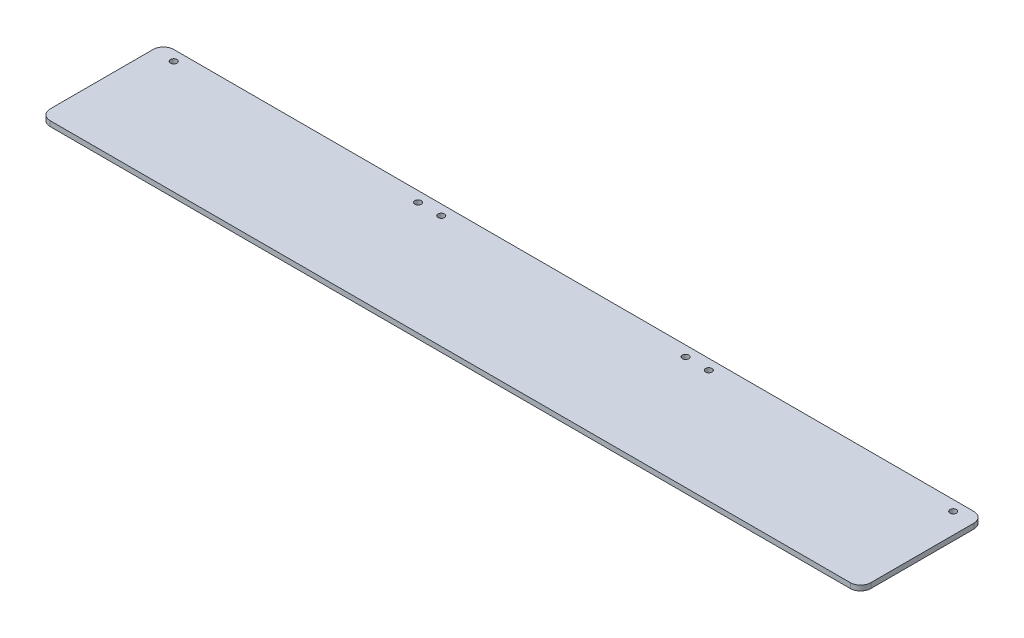
SolidWorks part; units mm, degrees
material "PC High Viscosity"
ref_plane "Front Plane" through (0, 0, 0) normal (0, 0, 1) x (1, 0, 0)
ref_plane "Top Plane" through (0, 0, 0) normal (0, 1, 0) x (1, 0, 0)
ref_plane "Right Plane" through (0, 0, 0) normal (1, 0, 0) x (0, 0, -1)
sketch "Sketch1" plane through (0, 0, 0) normal (0, 1, 0) x (1, 0, 0)
  line L0 (654.05, 279.4) -> (711.2, 279.4) construction
  line L1 (25.4, 0) -> (2000.25, 0)
  line L2 (0, 25.4) -> (0, 279.4)
  line L3 (25.4, 304.8) -> (2000.25, 304.8)
  line L4 (2025.65, 25.4) -> (2025.65, 279.4)
  line L17 (1012.825, 304.8) -> (1012.825, 0) construction
  line L28 (50.8, 279.4) -> (50.8, 304.8) construction
  line L30 (1974.85, 279.4) -> (1974.85, 304.8) construction
  line L32 (1371.6, 279.4) -> (1314.45, 279.4) construction
  arc A0 (2000.25, 304.8) -> (2025.65, 279.4) centre (2000.25, 279.4) cw
  arc A3 (0, 279.4) -> (25.4, 304.8) centre (25.4, 279.4) cw
  circle A4 centre (50.8, 279.4) radius 7.9375
  circle A10 centre (654.05, 279.4) radius 7.9375
  circle A12 centre (711.2, 279.4) radius 7.9375
  circle A42 centre (1314.45, 279.4) radius 7.9375
  circle A43 centre (1371.6, 279.4) radius 7.9375
  circle A45 centre (1974.85, 279.4) radius 7.9375
  circle A46 centre (654.05, 88.9) radius 7.9375 [skipped]
  circle A47 centre (711.2, 88.9) radius 7.9375 [skipped]
  arc A50 (0, 25.4) -> (25.4, 0) centre (25.4, 25.4) ccw
  arc A51 (2025.65, 25.4) -> (2000.25, 0) centre (2000.25, 25.4) cw
  point P7 (2025.65, 304.8)
  point P12 (0, 0)
  point P15 (0, 304.8)
  point P93 (1371.6, 303.2125)
  point P105 (1371.6, 303.2125)
  point P112 (1371.6, 303.2125)
  point P119 (1371.6, 303.2125)
  point P126 (1371.6, 303.2125)
  point P133 (1371.6, 303.2125)
  point P140 (1371.6, 303.2125)
  point P147 (1371.6, 303.2125)
  point P154 (1371.6, 303.2125)
  point P161 (1371.6, 303.2125)
  point P168 (1371.6, 303.2125)
  point P175 (1371.6, 303.2125)
  point P182 (1371.6, 303.2125)
  point P189 (1371.6, 303.2125)
  point P196 (1371.6, 303.2125)
  point P203 (1371.6, 303.2125)
  point P210 (1371.6, 303.2125)
  point P217 (1371.6, 303.2125)
  point P224 (1371.6, 303.2125)
  point P231 (1371.6, 303.2125)
  dimension "D3" = 25.4
  dimension "D6" = 15.875
  dimension "D18" = 2
  dimension "D8" = 25.4
  dimension "D9" = 25.4
  dimension "D1" = 2025.65
  dimension "D2" = 304.8
  dimension "D4" = 50.8
  dimension "D5" = 25.4
  dimension "D20" = 57.15
  dimension "D7" = 654.05
  dimension "D19" = 2
extrude "Boss-Extrude1" add sketch "Sketch1" along normal blind 12.7
